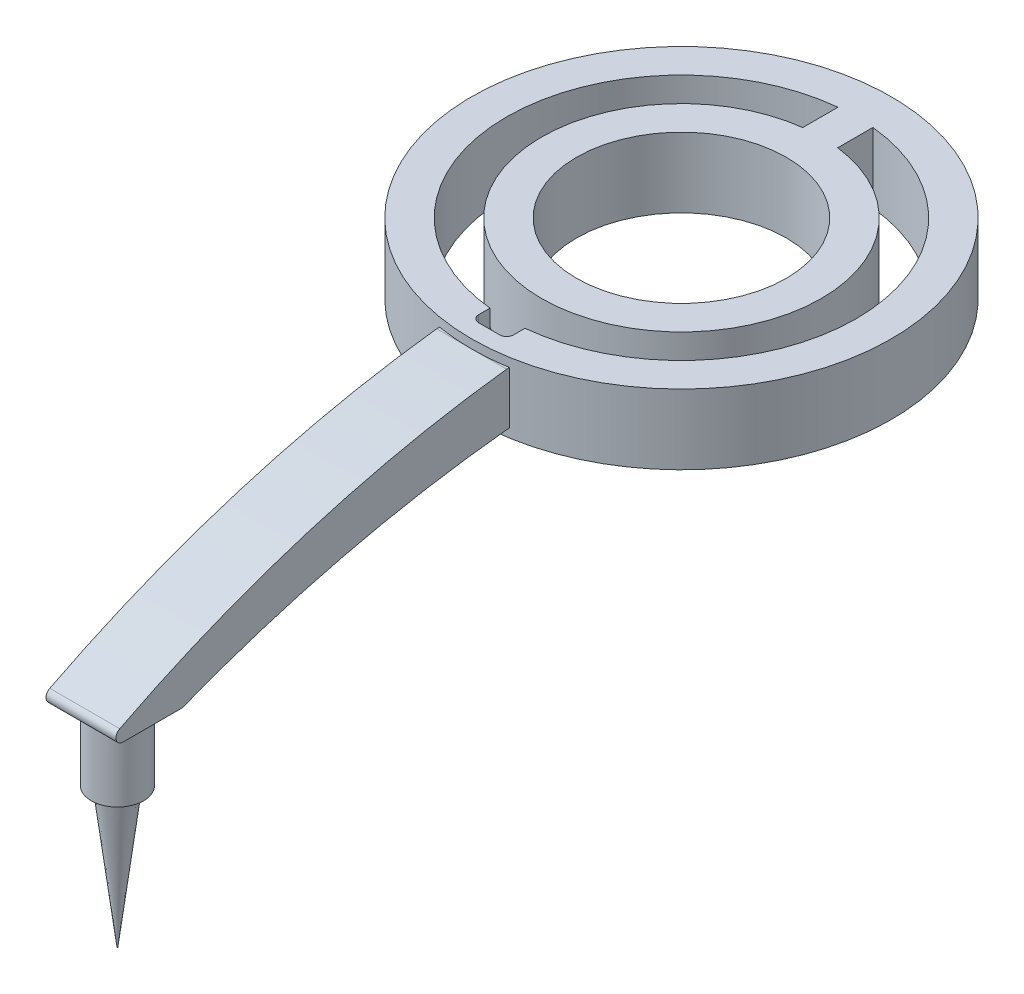
SolidWorks part; units mm, degrees
ref_plane "Front Plane" through (0, 0, 0) normal (0, 0, 1) x (1, 0, 0)
ref_plane "Top Plane" through (0, 0, 0) normal (0, 1, 0) x (1, 0, 0)
ref_plane "Right Plane" through (0, 0, 0) normal (1, 0, 0) x (0, 0, -1)
sketch "Sketch1" plane through (0, 0, 0) normal (0, 1, 0) x (1, 0, 0)
  line L2 (-2.5, 27.226) -> (-2.5, 16.7283)
  line L4 (2.5, 27.226) -> (2.5, 16.7283)
  line L5 (-2.5, -22.9334) -> (2.5, -22.9334)
  line L6 (-2.5, -22.9334) -> (-2.5, -26.5)
  line L7 (-1.5, -27.5) -> (1.5, -27.5)
  line L8 (2.5, -22.9334) -> (2.5, -26.5)
  arc A0 (-2.5, 19.8431) -> (2.5, 19.8431) centre (0, 0) ccw
  arc A1 (-2.5, 24.8747) -> (2.5, 24.8747) centre (0, 0) ccw
  circle A2 centre (0, 0) radius 30
  circle A3 centre (0, 0) radius 15
  arc A4 (-2.5, -26.5) -> (-1.5, -27.5) centre (-1.5, -26.5) ccw
  arc A5 (1.5, -27.5) -> (2.5, -26.5) centre (1.5, -26.5) ccw
  point P18 (-2.5, -27.5)
  point P21 (2.5, -27.5)
  dimension "D1" = 40
  dimension "D2" = 50
  dimension "D3" = 60
  dimension "D4" = 30
  dimension "D10" = 1
  dimension "D5" = 5
  dimension "D6" = 2.5
  dimension "D7" = 27.5
  dimension "D8" = 5
  dimension "D9" = 2.5
extrude "Boss-Extrude1" add sketch "Sketch1" along normal blind 10
sketch "Sketch2" plane through (0, 0, 0) normal (1, 0, 0) x (0, 0, -1)
  line L2 (-30, 10) -> (-30, 0) construction
  line L3 (30, 10) -> (-30, 10) construction
  line L4 (-84.8616, -10) -> (-76.4, -10)
  line L7 (-30, 8.75) -> (-27.5, 8.75)
  line L9 (-30, 1.25) -> (-27.5, 1.25)
  line L10 (-27.5, 8.75) -> (-27.5, 1.25)
  arc A0 (-30, 1.25) -> (-76.4, -10) centre (-11.6727, -175.6521) ccw
  arc A1 (-30, 8.75) -> (-85.3173, -8.1098) centre (-10.6033, -154.0687) ccw
  arc A2 (-85.3173, -8.1098) -> (-84.8616, -10) centre (-84.8616, -9) ccw
  point P17 (-88.9, -10)
  dimension "D4" = 58.9
  dimension "D2" = 1
  dimension "D1" = 12.5
  dimension "D3" = 1.25
  dimension "D5" = 10
  dimension "D6" = 2.5
  dimension "D7" = 7.5
extrude "Boss-Extrude2" add sketch "Sketch2" along normal mid plane 10
sketch "Sketch3" plane through (0, -10, 0) normal (0, -1, 0) x (-1, 0, 0)
  line L0 (5, -84.8616) -> (5, -76.4) construction
  line L5 (-5, -76.4) -> (5, -76.4) construction
  circle A0 centre (0, -80.65) radius 3.75
  dimension "D1" = 7.5
  dimension "D2" = 5
  dimension "D3" = 4.25
extrude "Boss-Extrude3" add sketch "Sketch3" along normal blind 10
sketch "Sketch5" plane through (0, -20, 0) normal (0, -1, 0) x (-1, 0, 0)
  circle A0 centre (0, -80.65) radius 2.5
  dimension "D1" = 5
extrude "Boss-Extrude4" add sketch "Sketch5" along normal blind 20 draft 7
